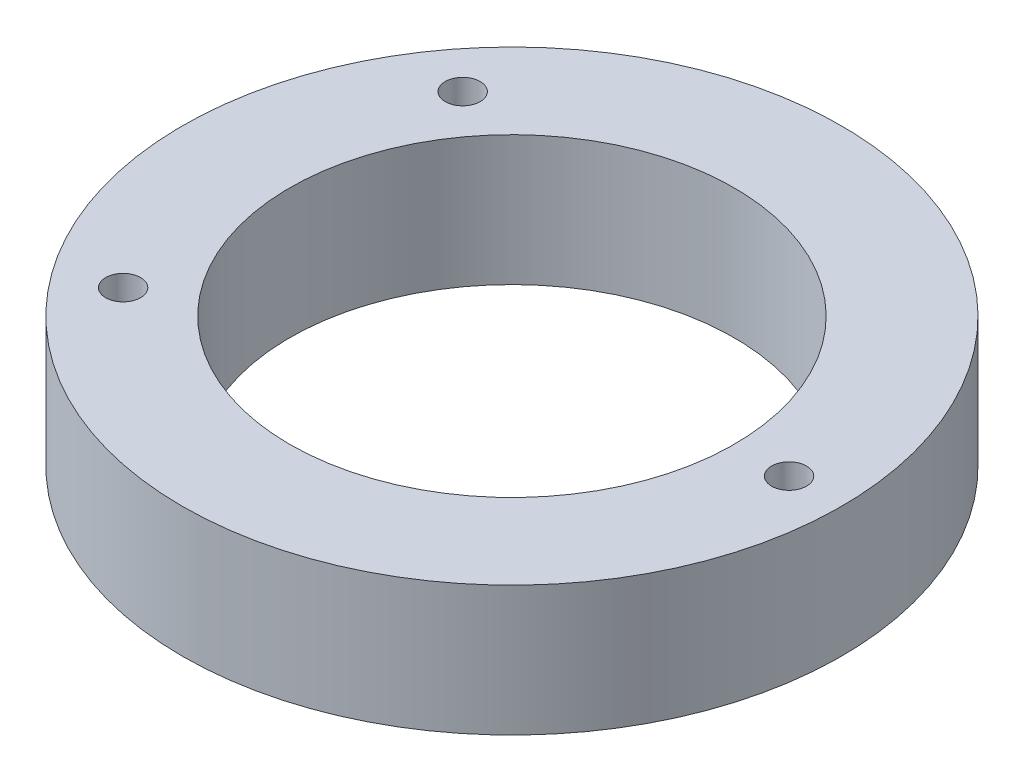
SolidWorks part; units mm, degrees
ref_plane "Front Plane" through (0, 0, 0) normal (0, 0, 1) x (1, 0, 0)
ref_plane "Top Plane" through (0, 0, 0) normal (0, 1, 0) x (1, 0, 0)
ref_plane "Right Plane" through (0, 0, 0) normal (1, 0, 0) x (0, 0, -1)
sketch "Sketch2" plane through (0, 0, 0) normal (0, 1, 0) x (1, 0, 0)
  line L0 (-21.9327, 17.0005) -> (0, 0) construction
  line L1 (0, 0) -> (-21.9327, -17.0005) construction
  line L2 (0, 0) -> (27.75, 0) construction
  line L3 (-21.9327, 17.0005) -> (-21.9327, -17.0005) construction
  circle A0 centre (0, 0) radius 22.25
  circle A1 centre (0, 0) radius 33
  circle A2 centre (-21.9327, 17.0005) radius 1.75
  circle A3 centre (-21.9327, -17.0005) radius 1.75
  circle A4 centre (27.75, 0) radius 1.75
  dimension "D1" = 44.5
  dimension "D2" = 66
  dimension "D5" = 3.5
  dimension "D3" = 75.56
  dimension "D4" = 27.75
extrude "Boss-Extrude1" add sketch "Sketch2" along normal blind 13
